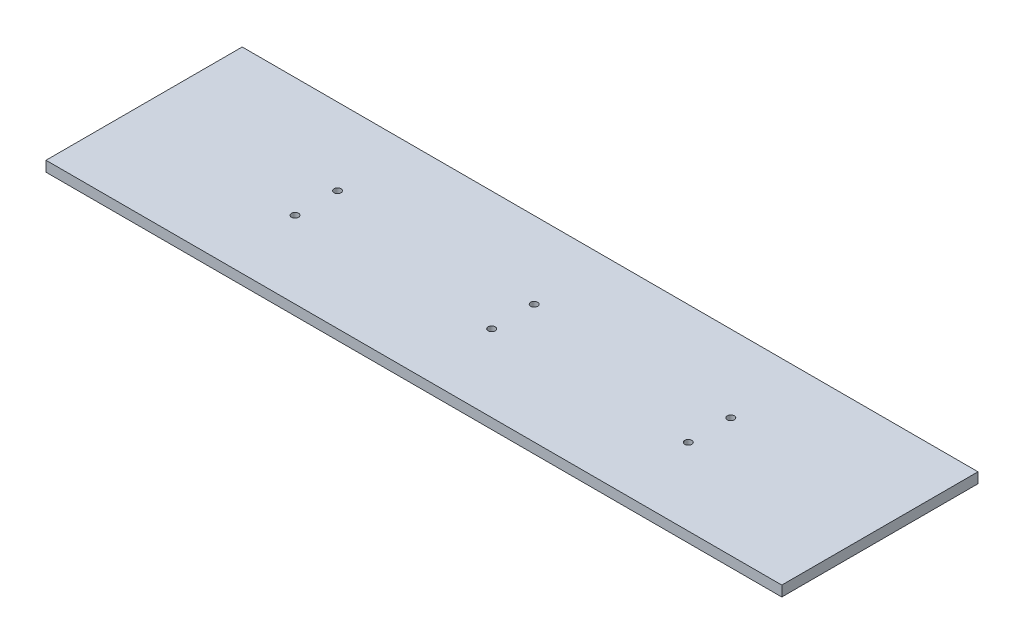
SolidWorks part; units mm, degrees
ref_plane "Front Plane" through (0, 0, 0) normal (0, 0, 1) x (1, 0, 0)
ref_plane "Top Plane" through (0, 0, 0) normal (0, 1, 0) x (1, 0, 0)
ref_plane "Right Plane" through (0, 0, 0) normal (1, 0, 0) x (0, 0, -1)
sketch "Sketch1" plane through (0, 0, 0) normal (0, 1, 0) x (1, 0, 0)
  line L1 (0, 0) -> (450, 0)
  line L2 (0, 0) -> (0, 120)
  line L3 (0, 120) -> (450, 120)
  line L4 (450, 0) -> (450, 120)
  line L5 (225.56, 73) -> (105.31, 73) construction
  line L6 (345.81, 47) -> (225.56, 47) construction
  line L7 (345.81, 73) -> (225.56, 73) construction
  line L8 (225.56, 47) -> (105.31, 47) construction
  circle A0 centre (345.81, 47) radius 2.16
  circle A1 centre (225.56, 47) radius 2.16
  circle A2 centre (105.31, 47) radius 2.16
  circle A3 centre (105.31, 73) radius 2.16
  circle A4 centre (225.56, 73) radius 2.16
  circle A5 centre (345.81, 73) radius 2.16
extrude "Boss-Extrude1" add sketch "Sketch1" along normal blind 6.35
